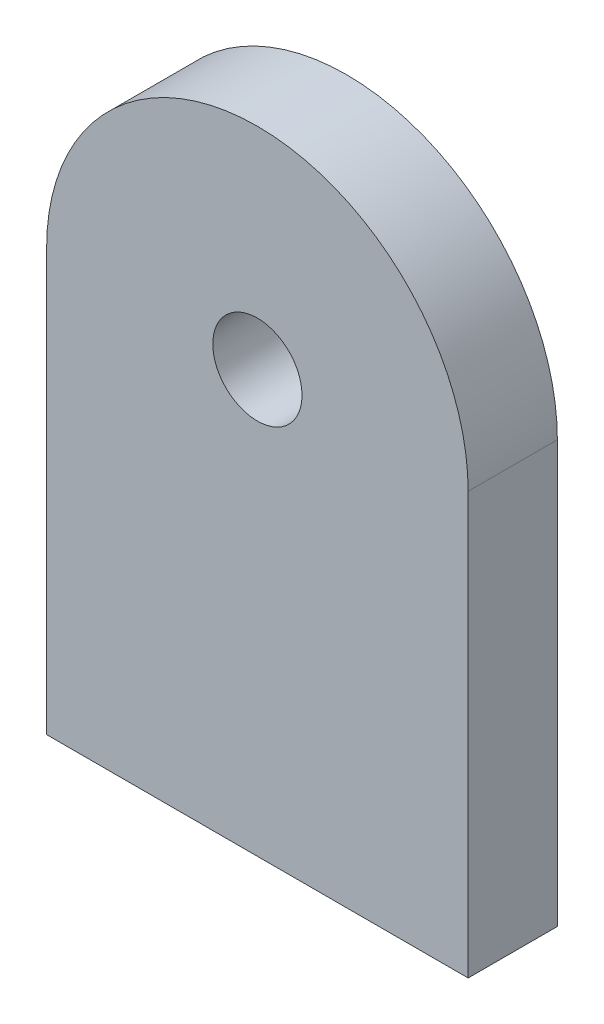
SolidWorks part; units mm, degrees
material "Balsa"
ref_plane "Front Plane" through (0, 0, 0) normal (0, 0, 1) x (1, 0, 0)
ref_plane "Top Plane" through (0, 0, 0) normal (0, 1, 0) x (1, 0, 0)
ref_plane "Right Plane" through (0, 0, 0) normal (1, 0, 0) x (0, 0, -1)
sketch "Sketch1" plane through (0, 0, 0) normal (0, 0, 1) x (1, 0, 0)
  line L1 (0, 0) -> (30, 0)
  line L2 (0, 0) -> (0, 30)
  line L4 (30, 0) -> (30, 30)
  arc A0 (0, 30) -> (30, 30) centre (15, 30) cw
  dimension "D1" = 30
  dimension "D2" = 30
extrude "main shape" add sketch "Sketch1" along normal blind 6.35
sketch "Sketch2" plane through (0, 0, 0) normal (0, 0, 1) x (1, 0, 0)
  line L0 (15, 0) -> (15, 45) construction
  line L1 (0, 0) -> (30, 0) construction
  arc A0 (30, 30) -> (0, 30) centre (15, 30) ccw construction
  point P7 (15, 30)
  dimension "D1" = 30
hole_wizard "1/4 (0.25) Diameter Hole1" positions "Sketch4" profile "Sketch3" hole size "1/4" standard "Ansi Inch"
sketch "Sketch4" plane through (0, 0, 6.35) normal (0, 0, 1) x (1, 0, 0)
  point P1 (15, 30)
sketch "Sketch3" plane through (15, 30, 6.35) normal (1, 0, 0) x (0, -1, 0)
  line L0 (0, 0) -> (0, 19.9077)
  line L1 (0, 19.9077) -> (3.175, 18)
  line L2 (3.175, 18) -> (3.175, 0)
  line L5 (3.175, 0) -> (0, 0)
  line L10 (0, 19.9077) -> (-3.175, 18) construction
  line L11 (0, -6.35) -> (0, 107.95) construction
  dimension "Hole Dia." = 6.35
  dimension "Hole Depth" = 18
  dimension "Drill Angle" = 118
